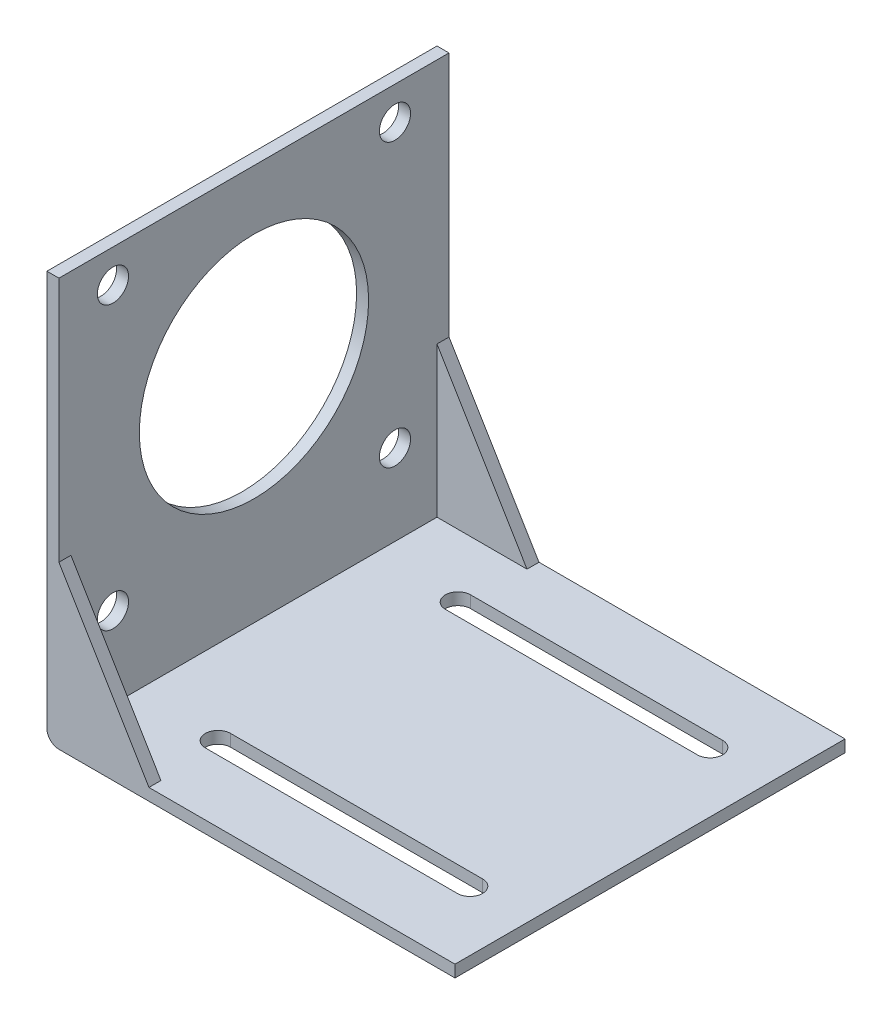
SolidWorks part; units mm, degrees
ref_plane "Спереди" through (0, 0, 0) normal (0, 0, 1) x (1, 0, 0)
ref_plane "Сверху" through (0, 0, 0) normal (0, 1, 0) x (1, 0, 0)
ref_plane "Справа" through (0, 0, 0) normal (1, 0, 0) x (0, 0, -1)
sketch "Эскиз1" plane through (0, 0, 0) normal (0, 0, 1) x (1, 0, 0)
  line L0 (2, 0) -> (68, 0)
  line L1 (0, 2) -> (0, 68)
  line L2 (0, 68) -> (2, 68)
  line L3 (2, 68) -> (2, 2)
  line L4 (2, 2) -> (68, 2)
  line L5 (68, 2) -> (68, 0)
  arc A0 (2, 0) -> (0, 2) centre (2, 2) cw
  dimension "D1" = 2
extrude "Бобышка-Вытянуть1" add sketch "Эскиз1" along normal blind 65
sketch "Эскиз2" plane through (2, 0, 0) normal (1, 0, 0) x (0, 0, -1)
  line L0 (-77.9027, 68) -> (-77.9027, 39) construction
  line L2 (-56, 15.5) -> (-9, 15.5) construction
  line L3 (-56, 15.5) -> (-56, 62.5) construction
  line L4 (-56, 62.5) -> (-9, 62.5) construction
  line L5 (-9, 15.5) -> (-9, 62.5) construction
  line L6 (-56, 15.5) -> (-9, 62.5) construction
  line L7 (-56, 62.5) -> (-9, 15.5) construction
  circle A0 centre (-32.5, 39) radius 19.1
  circle A1 centre (-9, 62.5) radius 2.6
  circle A2 centre (-9, 15.5) radius 2.6
  circle A3 centre (-56, 15.5) radius 2.6
  circle A4 centre (-56, 62.5) radius 2.6
  dimension "D2" = 38.2
  dimension "D4" = 5.2
  dimension "D5" = 5.2
  dimension "D6" = 5.2
  dimension "D7" = 5.2
  dimension "D1" = 29
  dimension "D3" = 47
extrude "Вырез-Вытянуть1" cut sketch "Эскиз2" against normal through all
sketch "Эскиз3" plane through (0, 2, 0) normal (0, 1, 0) x (1, 0, 0)
  line L0 (68, 6.3687) -> (58, 6.3687) construction
  line L1 (76.0115, -12.5) -> (76.0115, -52.5) construction
  line L2 (58, -12.5) -> (16, -12.5) construction
  line L3 (58, -52.5) -> (16, -52.5) construction
  line L4 (16, -12.5) -> (58, -12.5) construction
  line L5 (16, -10.4) -> (58, -10.4)
  line L6 (16, -14.6) -> (58, -14.6)
  line L7 (16, -52.5) -> (58, -52.5) construction
  line L8 (16, -50.4) -> (58, -50.4)
  line L9 (16, -54.6) -> (58, -54.6)
  arc A0 (16, -10.4) -> (16, -14.6) centre (16, -12.5) ccw
  arc A1 (58, -14.6) -> (58, -10.4) centre (58, -12.5) ccw
  arc A2 (16, -50.4) -> (16, -54.6) centre (16, -52.5) ccw
  arc A3 (58, -54.6) -> (58, -50.4) centre (58, -52.5) ccw
  point P8 (37, -12.5)
  point P13 (37, -52.5)
  dimension "D1" = 10
  dimension "D2" = 40
  dimension "D3" = 42
  dimension "D4" = 42
extrude "Вырез-Вытянуть2" cut sketch "Эскиз3" against normal through all
sketch "Эскиз4" plane through (0, 0, 65) normal (0, 0, 1) x (1, 0, 0)
  line L0 (-3.2681, 2) -> (-3.2681, 27) construction
  line L1 (2, -3.2208) -> (17, -3.2208) construction
  line L2 (2, 27) -> (17, 2)
  line L3 (2, 2) -> (2, 68) construction
  line L4 (17, 2) -> (2, 2)
  line L5 (2, 2) -> (2, 27)
  dimension "D1" = 25
  dimension "D2" = 15
extrude "Бобышка-Вытянуть2" add sketch "Эскиз4" against normal blind 2
sketch "Эскиз5" plane through (0, 0, 0) normal (0, 0, -1) x (-1, 0, 0)
  line L0 (-2, 27) -> (-17, 2)
  line L1 (-17, 2) -> (-2, 2)
  line L2 (-2, 2) -> (-2, 27)
extrude "Бобышка-Вытянуть3" add sketch "Эскиз5" against normal blind 2
